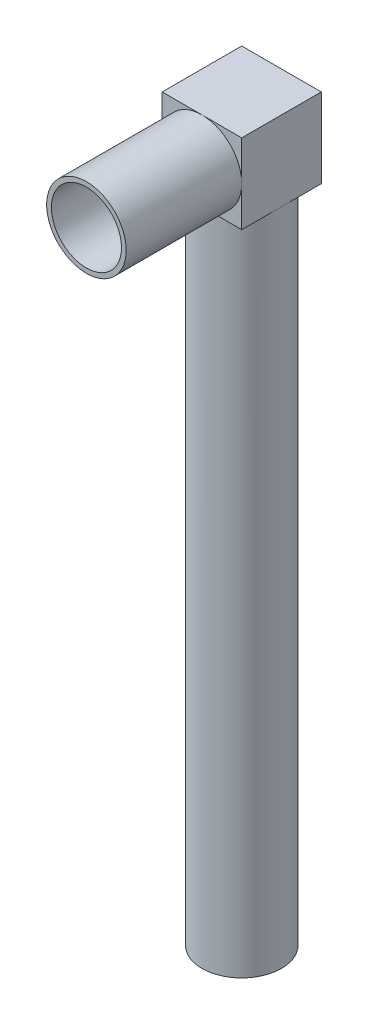
SolidWorks part; units mm, degrees
ref_plane "Front Plane" through (0, 0, 0) normal (0, 0, 1) x (1, 0, 0)
ref_plane "Top Plane" through (0, 0, 0) normal (0, 1, 0) x (1, 0, 0)
ref_plane "Right Plane" through (0, 0, 0) normal (1, 0, 0) x (0, 0, -1)
sketch "Sketch1" plane through (0, 0, 0) normal (0, 0, 1) x (1, 0, 0)
  circle A0 centre (0, 0) radius 21.1
  circle A1 centre (0, 0) radius 18.6
extrude "Boss-Extrude4" add sketch "Sketch1" along normal blind 58.8
sketch "Sketch4" plane through (0, 0, 0) normal (0, 0, -1) x (-1, 0, 0)
  circle A0 centre (0, 0) radius 21.1
extrude "Boss-Extrude5" add sketch "Sketch4" along normal blind 2.5
sketch3d "3DSketch1"
  circle A0 centre (0, 0, 18.6) radius 21.1
  point P3 (0, 0, 0)
  point P6 (0, 21.1, 18.6)
  point P7 (0, 0, 0)
sketch "Sketch12" plane through (0, 0, -2.5) normal (0, 0, -1) x (-1, 0, 0)
  line L1 (-21.1, -21.1) -> (21.1, -21.1)
  line L2 (-21.1, -21.1) -> (-21.1, 21.1)
  line L3 (-21.1, 21.1) -> (21.1, 21.1)
  line L4 (21.1, -21.1) -> (21.1, 21.1)
  line L5 (-21.1, -21.1) -> (21.1, 21.1) construction
  line L6 (-21.1, 21.1) -> (21.1, -21.1) construction
  point P0 (0, 0)
extrude "Boss-Extrude6" add sketch "Sketch12" along normal blind 42.2
sketch "Sketch13" plane through (0, -21.1, 0) normal (0, -1, 0) x (-1, 0, 0)
  circle A0 centre (0, 23.6) radius 21.1
extrude "Boss-Extrude7" add sketch "Sketch13" along normal blind 350
sketch "Sketch14" plane through (0, -371.1, 0) normal (0, -1, 0) x (-1, 0, 0)
  line L3 (-1.6853, 21.1) -> (1.6853, 21.1)
  arc A1 (-1.6853, 21.1) -> (1.6853, 21.1) centre (0, 23.6) cw
  point P0 (0, 0)
extrude "Cut-Extrude1" cut sketch "Sketch14" against normal blind 21.5
sketch "Sketch15" plane through (0, -371.1, 0) normal (0, -1, 0) x (-1, 0, 0)
  circle A0 centre (0, 23.6) radius 3
extrude "Cut-Extrude2" cut sketch "Sketch15" against normal blind 9.5
sketch "Sketch16" plane through (0, -371.1, 0) normal (0, -1, 0) x (-1, 0, 0)
  circle A0 centre (0, 23.6) radius 6.025
extrude "Cut-Extrude3" cut sketch "Sketch16" against normal blind 6.2
sketch "Sketch17" plane through (0, 0, -44.7) normal (0, 0, -1) x (-1, 0, 0)
  line L1 (-18.6, -18.6) -> (18.6, -18.6)
  line L2 (-18.6, -18.6) -> (-18.6, 18.6)
  line L3 (-18.6, 18.6) -> (18.6, 18.6)
  line L4 (18.6, -18.6) -> (18.6, 18.6)
  line L5 (-18.6, -18.6) -> (18.6, 18.6) construction
  line L6 (-18.6, 18.6) -> (18.6, -18.6) construction
  point P0 (0, 0)
extrude "Cut-Extrude4" cut sketch "Sketch17" against normal blind 39.7
sketch "Sketch18" plane through (0, 0, 0) normal (0, 0, 1) x (1, 0, 0)
  circle A0 centre (0, 0) radius 15
extrude "Cut-Extrude5" cut sketch "Sketch18" against normal blind 5
sketch "Sketch19" plane through (0, -21.1, 0) normal (0, -1, 0) x (-1, 0, 0)
  circle A2 centre (-16.7725, 40.3725) radius 1.8275
extrude "Cut-Extrude6" cut sketch "Sketch19" against normal blind 2.5 contours A2
sketch "Sketch23" plane through (0, -21.1, 0) normal (0, -1, 0) x (-1, 0, 0)
  circle A0 centre (-0.6541, 23.6) radius 17.9459
  point P0 (0, 0)
extrude "Cut-Extrude7" cut sketch "Sketch23" against normal blind 2.5
